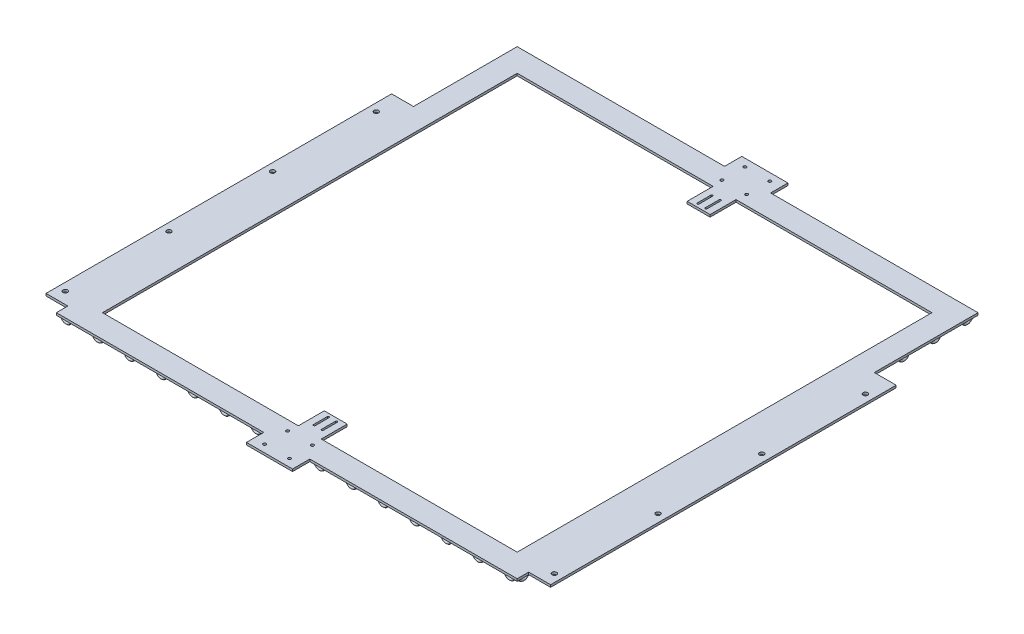
SolidWorks part; units mm, degrees
ref_plane "前视基准面" through (0, 0, 0) normal (0, 0, 1) x (1, 0, 0)
ref_plane "上视基准面" through (0, 0, 0) normal (0, 1, 0) x (1, 0, 0)
ref_plane "右视基准面" through (0, 0, 0) normal (1, 0, 0) x (0, 0, -1)
sketch "草图1" plane through (0, 0, 0) normal (0, 1, 0) x (1, 0, 0)
  line L0 (-400, 0) -> (-40, 0)
  line L1 (400, 800) -> (40, 800)
  line L2 (-400, 800) -> (-400, 0)
  line L3 (400, 0) -> (40, 0)
  line L4 (400, 800) -> (400, 0)
  line L5 (40, 0) -> (40, -30)
  line L6 (5.45, 55.0019) -> (5.45, 79.0019)
  line L7 (-360, 40) -> (-360, 760)
  line L8 (8.65, 79.0019) -> (8.65, 55.0019)
  line L9 (360, 760) -> (360, 40)
  line L10 (-400, 400) -> (400, 400) construction
  line L11 (-5.45, 79.0019) -> (-5.45, 55.0019)
  line L12 (-8.65, 55.0019) -> (-8.65, 79.0019)
  line L13 (40, -30) -> (-40, -30)
  line L14 (-360, 40) -> (-40, 40)
  line L15 (40, 800) -> (40, 830)
  line L16 (40, 830) -> (-40, 830)
  line L17 (360, 40) -> (40, 40)
  line L18 (-360, 40) -> (-40, 40)
  line L19 (-400, 800) -> (-40, 800)
  line L20 (-438, 20) -> (-400, 20)
  line L21 (360, 40) -> (40, 40)
  line L22 (-438, 620) -> (-400, 620)
  line L23 (8.65, 55.0019) -> (8.65, 79.0019)
  line L24 (5.45, 79.0019) -> (5.45, 55.0019)
  line L25 (-8.65, 79.0019) -> (-8.65, 55.0019)
  line L26 (-5.45, 55.0019) -> (-5.45, 79.0019)
  line L27 (0, 650) -> (0, 150) construction
  line L28 (-438, 20) -> (-438, 620)
  line L29 (438, 20) -> (400, 20)
  line L30 (-40, -30) -> (-40, 0)
  line L31 (-40, 40) -> (-19.9004, 40)
  line L32 (-5.45, 744.9981) -> (-5.45, 720.9981)
  line L33 (-8.65, 720.9981) -> (-8.65, 744.9981)
  line L34 (5.45, 720.9981) -> (5.45, 744.9981)
  line L35 (8.65, 744.9981) -> (8.65, 720.9981)
  line L36 (-19.9004, 40) -> (-19.9004, 85)
  line L37 (360, 760) -> (40, 760)
  line L38 (-19.9004, 85) -> (19.9004, 85)
  line L39 (19.9004, 85) -> (19.9004, 40)
  line L40 (-360, 760) -> (-40, 760)
  line L41 (360, 760) -> (40, 760)
  line L42 (19.9004, 40) -> (40, 40)
  line L43 (-40, 830) -> (-40, 800)
  line L44 (-360, 760) -> (-40, 760)
  line L45 (-40, 760) -> (-19.9004, 760)
  line L46 (-8.65, 744.9981) -> (-8.65, 720.9981)
  line L47 (-5.45, 720.9981) -> (-5.45, 744.9981)
  line L48 (8.65, 720.9981) -> (8.65, 744.9981)
  line L49 (5.45, 744.9981) -> (5.45, 720.9981)
  line L50 (-19.9004, 760) -> (-19.9004, 715)
  line L51 (19.9004, 760) -> (40, 760)
  line L52 (19.9004, 715) -> (19.9004, 760)
  line L53 (-19.9004, 715) -> (19.9004, 715)
  line L54 (438, 20) -> (438, 620)
  line L55 (438, 620) -> (400, 620)
  arc A0 (5.45, 79.0019) -> (8.65, 79.0019) centre (7.05, 79.0019) cw
  arc A1 (8.65, 55.0019) -> (5.45, 55.0019) centre (7.05, 55.0019) cw
  arc A2 (-5.45, 55.0019) -> (-8.65, 55.0019) centre (-7.05, 55.0019) cw
  arc A3 (-8.65, 79.0019) -> (-5.45, 79.0019) centre (-7.05, 79.0019) cw
  circle A4 centre (21.5, 23.0019) radius 2.5
  circle A5 centre (21.5, -16.9981) radius 2.5
  circle A7 centre (-21.5, 23.0019) radius 2.5
  circle A9 centre (-21.5, -16.9981) radius 2.5
  arc A10 (8.65, 79.0019) -> (5.45, 79.0019) centre (7.05, 79.0019) ccw
  arc A11 (5.45, 55.0019) -> (8.65, 55.0019) centre (7.05, 55.0019) ccw
  arc A12 (-8.65, 55.0019) -> (-5.45, 55.0019) centre (-7.05, 55.0019) ccw
  arc A13 (-5.45, 79.0019) -> (-8.65, 79.0019) centre (-7.05, 79.0019) ccw
  circle A14 centre (21.5, -16.9981) radius 2.5
  circle A16 centre (21.5, 23.0019) radius 2.5
  circle A18 centre (-21.5, -16.9981) radius 2.5
  circle A19 centre (-21.5, 23.0019) radius 2.5
  circle A20 centre (-21.5, 776.9981) radius 2.5
  circle A21 centre (-21.5, 816.9981) radius 2.5
  circle A23 centre (21.5, 776.9981) radius 2.5
  circle A25 centre (21.5, 816.9981) radius 2.5
  arc A26 (-5.45, 720.9981) -> (-8.65, 720.9981) centre (-7.05, 720.9981) cw
  arc A27 (-8.65, 744.9981) -> (-5.45, 744.9981) centre (-7.05, 744.9981) cw
  arc A28 (5.45, 744.9981) -> (8.65, 744.9981) centre (7.05, 744.9981) cw
  arc A29 (8.65, 720.9981) -> (5.45, 720.9981) centre (7.05, 720.9981) cw
  circle A30 centre (-21.5, 816.9981) radius 2.5
  circle A32 centre (-21.5, 776.9981) radius 2.5
  circle A34 centre (21.5, 816.9981) radius 2.5
  circle A35 centre (21.5, 776.9981) radius 2.5
  arc A36 (-8.65, 720.9981) -> (-5.45, 720.9981) centre (-7.05, 720.9981) ccw
  arc A37 (-5.45, 744.9981) -> (-8.65, 744.9981) centre (-7.05, 744.9981) ccw
  arc A38 (8.65, 744.9981) -> (5.45, 744.9981) centre (7.05, 744.9981) ccw
  arc A39 (5.45, 720.9981) -> (8.65, 720.9981) centre (7.05, 720.9981) ccw
extrude "凸台-拉伸1" add sketch "草图1" along normal blind 4
ref_plane "基准面1" through (0, 30, 0) normal (0, 1, 0) x (1, 0, 0)
ref_plane "基准面2" through (0, 4, 0) normal (0, 1, 0) x (1, 0, 0)
ref_plane "基准面3" through (0, 0, -6) normal (0, 0, 1) x (1, 0, 0)
sketch "草图12" plane through (0, 0, -6) normal (0, 0, 1) x (1, 0, 0)
  arc A0 (-396, 0) -> (-380, 0) centre (-388, 0) ccw
sketch "草图14" plane through (0, 0, 0) normal (0, 1, 0) x (1, 0, 0)
  circle A0 centre (-396, 6) radius 2
ref_plane "基准面5" through (5.0498, 0, 5.0498) normal (-0.7071, 0, -0.7071) x (-0.7071, 0, 0.7071)
ref_plane "基准面6" through (-394, 0, 0) normal (-1, 0, 0) x (0, 0, 1)
sketch "草图17" plane through (-394, 0, 0) normal (-1, 0, 0) x (0, 0, 1)
  arc A1 (-794.32, 0) -> (-778.32, 0) centre (-786.32, 0) ccw
sketch "草图18" plane through (0, 0, 0) normal (0, 1, 0) x (1, 0, 0)
  circle A0 centre (-394, 794.32) radius 2
sketch "草图19" plane through (0, 0, 0) normal (0, 1, 0) x (1, 0, 0)
  line L0 (0, 650) -> (0, 539.9992) construction
  circle A0 centre (-424.4982, 220) radius 4
  circle A1 centre (-424.4982, 400) radius 4
  circle A2 centre (-424.4982, 580) radius 4
  circle A3 centre (-424.4982, 40) radius 4
  circle A6 centre (424.4982, 40) radius 4
  circle A7 centre (424.4982, 580) radius 4
  circle A8 centre (424.4982, 400) radius 4
  circle A9 centre (424.4982, 220) radius 4
ref_plane "基准面7" through (0, 0, -400) normal (0, 0, 1) x (1, 0, 0)
extrude "切除-拉伸2" cut sketch "草图19" against normal mid plane 40
sweep "扫描1" add profiles "草图14" path "草图12"
sweep "扫描3" add profiles "草图18" path "草图17"
pattern_linear "阵列(线性)3" count 15 spacing 55 along (0, 0, 1) of "扫描3"
mirror "镜向1" about plane through (0, 0, 0) normal (1, 0, 0) of "阵列(线性)3", "扫描3"
pattern_linear "阵列(线性)4" count 15 spacing 55 along (1, 0, 0) skipping (7, 0) of "扫描1"
mirror "镜向2" about plane through (0, 0, -400) normal (0, 0, 1) of "阵列(线性)4", "扫描1"
sketch "草图20" plane through (0, 0, -6) normal (0, 0, 1) x (1, 0, 0)
  line L0 (390, 0) -> (374, 0)
  line L1 (382, 0) -> (382, -6)
  line L2 (319, 0) -> (335, 0)
  line L3 (327, 0) -> (327, -6)
